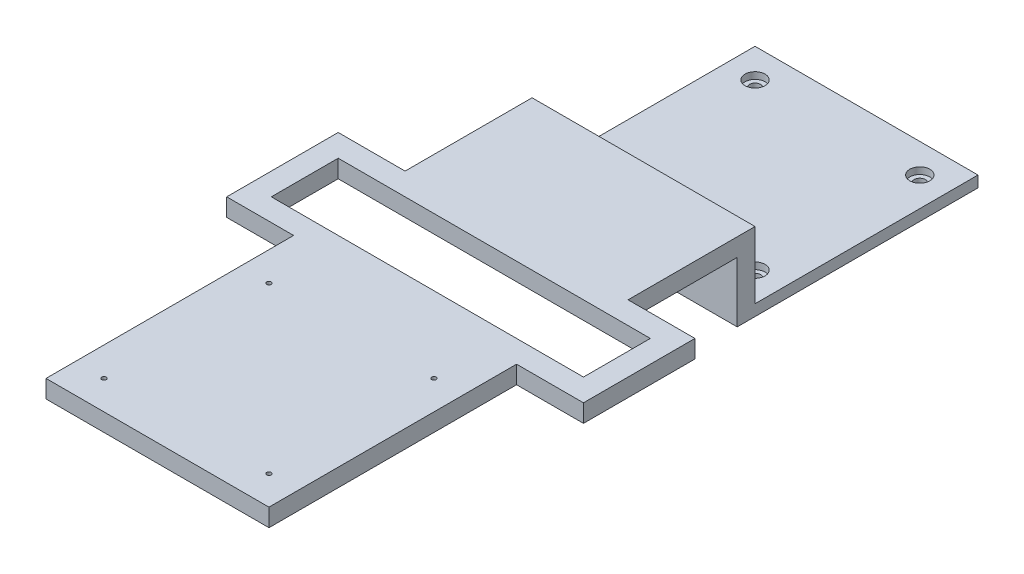
SolidWorks part; units mm, degrees
ref_plane "Front Plane" through (0, 0, 0) normal (0, 0, 1) x (1, 0, 0)
ref_plane "Top Plane" through (0, 0, 0) normal (0, 1, 0) x (1, 0, 0)
ref_plane "Right Plane" through (0, 0, 0) normal (1, 0, 0) x (0, 0, -1)
sketch "Sketch1" plane through (0, 0, 0) normal (0, 1, 0) x (1, 0, 0)
  line L0 (0, 44.3291) -> (0, -49.0863) construction
  line L1 (-50, 50) -> (50, 50)
  line L2 (-50, 50) -> (-50, -50)
  line L3 (-50, -50) -> (50, -50)
  line L4 (50, 50) -> (50, -50)
  line L5 (-50, 50) -> (50, -50) construction
  line L6 (-50, -50) -> (50, 50) construction
  line L7 (-55.6456, 0) -> (53.7715, 0) construction
  circle A0 centre (-36.95, 36.95) radius 2.5
  circle A1 centre (36.95, 36.95) radius 2.5
  circle A2 centre (36.95, -36.95) radius 2.5
  circle A3 centre (-36.95, -36.95) radius 2.5
  point P1 (0, 0)
  dimension "D1" = 73.9
  dimension "D2" = 73.9
  dimension "D4" = 5
  dimension "D3" = 100
extrude "Boss-Extrude1" add sketch "Sketch1" along normal blind 5
sketch "Sketch6" plane through (0, 0, 0) normal (0, -1, 0) x (1, 0, 0)
  line L0 (59.8047, 0) -> (-72.4197, 0) construction
  line L1 (0, 49.555) -> (0, -51.1902) construction
  circle A0 centre (-36.95, 36.95) radius 4.5
  circle A1 centre (36.95, 36.95) radius 4.5
  circle A2 centre (36.95, -36.95) radius 4.5
  circle A3 centre (-36.95, -36.95) radius 4.5
  dimension "D1" = 9
extrude "Cut-Extrude1" cut sketch "Sketch6" along normal blind 3 from surface at -5 starting at face at (36.95, 5, 39.45)
sketch "Sketch8" plane through (-50, 0, 0) normal (-1, 0, 0) x (0, 0, 1)
  line L1 (50, 0) -> (58, 0)
  line L2 (50, 0) -> (50, 35)
  line L3 (50, 35) -> (58, 35)
  line L4 (58, 0) -> (58, 35)
  dimension "D1" = 8
  dimension "D2" = 35
extrude "Boss-Extrude2" add sketch "Sketch8" against normal through all
sketch "Sketch9" plane through (0, 0, 58) normal (0, 0, 1) x (1, 0, 0)
  line L0 (50, 0) -> (50, 35) construction
  line L1 (-50, 35) -> (50, 35)
  line L2 (-50, 35) -> (-50, 27)
  line L3 (-50, 27) -> (50, 27)
  line L4 (50, 35) -> (50, 27)
  dimension "D1" = 8
extrude "Boss-Extrude3" add sketch "Sketch9" along normal blind 210
sketch "Sketch10" plane through (0, 35, 0) normal (0, 1, 0) x (1, 0, 0)
  line L0 (-50, -268) -> (-50, -50) construction
  line L1 (-80, -106.95) -> (80, -106.95)
  line L2 (-80, -106.95) -> (-80, -156.95)
  line L3 (-80, -156.95) -> (80, -156.95)
  line L4 (80, -106.95) -> (80, -156.95)
  line L5 (-80, -106.95) -> (80, -156.95) construction
  line L6 (-80, -156.95) -> (80, -106.95) construction
  line L7 (50, -268) -> (50, -50) construction
  circle A0 centre (36.95, -36.95) radius 2.5 construction
  point P0 (0, -131.95)
  point P9 (80, -66.0144)
  dimension "D1" = 30
  dimension "D2" = 30
  dimension "D3" = 50
  dimension "D4" = 70
extrude "Boss-Extrude4" add sketch "Sketch10" against normal up to surface (8 mm away) up to face at (0, 27, 163)
sketch "Sketch11" plane through (0, 35, 0) normal (0, 1, 0) x (1, 0, 0)
  line L1 (-70, -116.95) -> (70, -116.95)
  line L2 (-70, -116.95) -> (-70, -146.95)
  line L3 (-70, -146.95) -> (70, -146.95)
  line L4 (70, -116.95) -> (70, -146.95)
  line L5 (-70, -116.95) -> (70, -146.95) construction
  line L6 (-70, -146.95) -> (70, -116.95) construction
  line L8 (-80, -106.95) -> (80, -156.95) construction
  line L9 (80, -106.95) -> (-80, -156.95) construction
  point P0 (0, -131.95)
  point P7 (0, 0)
  point P14 (0, -131.95)
  dimension "D1" = 140
  dimension "D2" = 30
extrude "Cut-Extrude2" cut sketch "Sketch11" against normal up to surface (8 mm away) up to face at (0, 27, 142.3)
sketch "Sketch13" plane through (0, 35, 0) normal (0, 1, 0) x (1, 0, 0)
  line L5 (-37, -181) -> (37, -255) construction
  line L6 (-37, -255) -> (37, -181) construction
  line L7 (0, -276.3326) -> (0, -189.7195) construction
  line L12 (-28.4717, -218) -> (37, -218) construction
  circle A1 centre (-37, -181) radius 1
  circle A2 centre (37, -181) radius 1
  circle A3 centre (37, -255) radius 1
  circle A4 centre (-37, -255) radius 1
  point P0 (0, -218)
  dimension "D2" = 2
  dimension "D1" = 74
extrude "Cut-Extrude3" cut sketch "Sketch13" against normal up to surface (8 mm away) up to face at (0, 27, 131.95)
